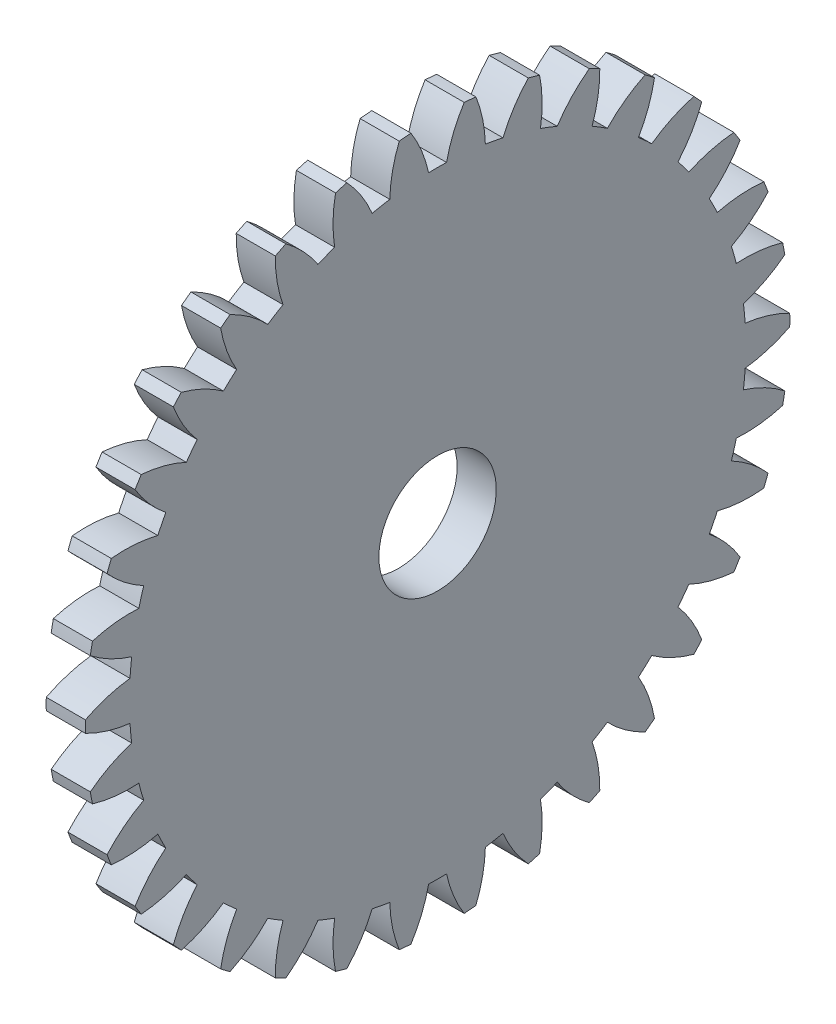
SolidWorks part; units mm, degrees
ref_plane "Plane1" through (0, 0, 0) normal (0, 0, 1) x (1, 0, 0)
ref_plane "Plane2" through (0, 0, 0) normal (0, 1, 0) x (1, 0, 0)
ref_plane "Plane3" through (0, 0, 0) normal (1, 0, 0) x (0, 0, -1)
sketch "HoldingSke" plane through (0, 0, 0) normal (0, 1, 0) x (1, 0, 0)
  line L0 (0, 0) -> (0.829, -0.5592)
  line L1 (-15, 0) -> (100, 0) construction
  line L2 (0, 0) -> (-2.1039, 2.3779)
  line L3 (0, 0) -> (-11.863, 4.5341)
  line L4 (0, 0) -> (7.1596, 4.8292)
  line L5 (0, 0) -> (-46.8476, -17.4728)
  line L6 (0, 0) -> (-1.6579, -1.1186)
  line L7 (-2.1039, 2.3779) -> (8.6586, 51.2059)
  line L8 (-76.2, 54.61) -> (-75.2, 54.61)
  line L9 (-71.009, 38.7566) -> (-53.1078, 45.2721)
  line L10 (-76.2, 71.12) -> (104.1128, 71.12)
  line L11 (0, 0) -> (-2, 0)
  line L12 (-76.2, 101.6) -> (-76.162, 101.6)
  line L13 (24.9733, 27.94) -> (52.9518, 28.4284)
  line L14 (24.9733, 27.94) -> (24.9743, 27.94)
  line L15 (24.9733, 27.94) -> (100.4006, 29.5858)
  line L16 (-63.627, -1) -> (-12.827, -1)
  circle A0 centre (0, 0) radius 3
  circle A1 centre (0, 0) radius 15.749
  circle A2 centre (0, 0) radius 37.5
  circle A3 centre (0, 0) radius 3
  dimension "MHD" = 31.498
  dimension "Hub_dia" = 75
  dimension "Bore" = 6
  dimension "MBD" = 6
  dimension "Num_teeth" = 34
  dimension "Pitch_radius" = 180.3128
  dimension "Pitch" = 1
  dimension "Width" = 2
  dimension "Overall_len" = 50
  dimension "Show_teeth" = 34
  dimension "Thickness" = 2
  dimension "OAL" = 50.0001
  dimension "T_dim" = 1
  dimension "Ap" = 20
  dimension "H" = 19.05
  dimension "Backlash" = 0.038
  dimension "Addendum_fac" = 1
  dimension "Dedendum_fac" = 1.25
  dimension "Clearance_fac" = 0.25
  dimension "Dedendum_add" = 0.001
  dimension "Module" = 1
sketch "BasProSke" plane through (0, 0, 0) normal (0, 1, 0) x (1, 0, 0)
  line L0 (-10, 0) -> (60, 0) construction
  line L1 (0, 0) -> (0, 18)
  line L2 (0, 0) -> (2, 0)
  line L3 (2, 0) -> (2, 18)
  line L4 (2, 18) -> (0, 18)
  dimension "Diameter" = 36
  dimension "Thickness" = 2
revolve "Base-Revolve" add sketch "BasProSke" angle 360 about L0
sketch "TooCutSke" plane through (0, 0, 0) normal (1, 0, 0) x (0, 0, -1)
  line L1 (0, 0) -> (0, 107) construction
  line L2 (0, 0) -> (-0.8516, 16.9787) construction
  line L3 (0, 0) -> (-3.1343, 33.8247) construction
  line L4 (-0.8516, 16.9787) -> (-1.5672, 16.9124) construction
  arc A0 (0.4581, 15.7423) -> (-0.4581, 15.7423) centre (0, 0) ccw
  arc A1 (1.3773, 17.9727) -> (-1.3773, 17.9727) centre (0, 0) ccw
  circle A2 centre (0, 0) radius 17 construction
  circle A3 centre (0, 0) radius 15.9748 construction
  arc A4 (-0.4581, 15.7423) -> (-1.3773, 17.9727) centre (-7.1051, 14.3077) ccw
  arc A5 (1.3773, 17.9727) -> (0.4581, 15.7423) centre (7.1051, 14.3077) ccw
  dimension "Root_dia" = 31.498
  dimension "Overcut_dia" = 36.0508
  dimension "Pitch_dia" = 34
  dimension "Base_dia" = 31.9495
  dimension "Flank_rad" = 6.8
  dimension "Half_ang" = 5.294
  dimension "Half_CT" = 0.7186
extrude "ToothCut" cut sketch "TooCutSke" along normal through all
fillet "Breaks" [suppressed] radius 0.02
fillet "RootFillets" [suppressed] radius 0.251
pattern_circular "TeethCuts" count 34 every 10.588 about axis through (-10, 0, 0) along (1, 0, 0) of "ToothCut", "RootFillets", "Breaks"
sketch "HubNeaOneSke" plane through (0, 0, 0) normal (-1, 0, 0) x (0, 0, 1)
  circle A0 centre (0, 0) radius 15.749
  dimension "Diameter" = 31.498
extrude "HubNearOne" [suppressed] add sketch "HubNeaOneSke" along normal blind 48.0001
sketch "HubNeaBotSke" plane through (0, 0, 0) normal (-1, 0, 0) x (0, 0, 1)
  circle A0 centre (0, 0) radius 15.749
  dimension "Diameter" = 31.498
extrude "HubNearBoth" [suppressed] add sketch "HubNeaBotSke" along normal blind 24
ref_plane "FarPln" through (2, 0, 0) normal (1, 0, 0) x (0, 0, -1)
sketch "HubFarSke" plane through (2, 0, 0) normal (1, 0, 0) x (0, 0, -1)
  circle A0 centre (0, 0) radius 15.749
  dimension "Diameter" = 31.498
extrude "HubFar" [suppressed] add sketch "HubFarSke" along normal blind 24
sketch "BorSke" plane through (0, 0, 0) normal (1, 0, 0) x (0, 0, -1)
  circle A0 centre (0, 0) radius 3
  dimension "Diameter" = 6
extrude "Bore" cut sketch "BorSke" along normal mid plane 100.0001
sketch "KeySke" plane through (0, 0, 0) normal (1, 0, 0) x (0, 0, -1)
  line L0 (-1, 0) -> (-1, 4)
  line L1 (-1, 4) -> (1, 4)
  line L2 (1, 4) -> (1, 0)
  line L3 (0, 0) -> (0, 34) construction
  line L4 (-1, 0) -> (1, 0)
  dimension "Offset" = 4
  dimension "Width" = 2
extrude "Keyway" [suppressed] cut sketch "KeySke" along normal mid plane 100.0001
pattern_circular "Keyway2" [suppressed] count 2 every 90 about axis through (-10, 0, 0) along (1, 0, 0)
equation "' \"Module@HoldingSke\" = 6.35"
equation "' \"Num_teeth@HoldingSke\" = 12"
equation "' \"Ap@HoldingSke\" =  20"
equation "' \"Width@HoldingSke\" = 0.5 * 25.4"
equation "' \"Hub_dia@HoldingSke\"= 1 * 25.4"
equation "' \"Overall_len@HoldingSke\" = 1.0 * 25.4"
equation "' \"Bore@HoldingSke\" = 0.75 * 25.4"
equation "' \"T_dim@HoldingSke\" = 0.1 * 25.4"
equation "' \"Width@KeySke\" = 0.25 * 25.4"
equation "' \"Show_teeth@HoldingSke\" = 13"
equation "' \"Backlash@HoldingSke\" = 0.009 * 25.4"
equation "' \"Addendum_fac@HoldingSke\" = 1.0"
equation "' \"Dedendum_fac@HoldingSke\" = 1.25"
equation "' \"Dedendum_add@HoldingSke\" = 0.00005 * 25.4"
equation "' \"Clearance_fac@HoldingSke\" = 0.25"
equation "\"Pitch@HoldingSke\" = 1 / \"Module@HoldingSke\""
equation "\"Overcut_dia@TooCutSke\" = (\"Num_teeth@HoldingSke\" + 2 * \"Addendum_fac@HoldingSke\") / \"Pitch@HoldingSke\" + 0.002 * 25.4"
equation "\"Pitch_dia@TooCutSke\" = \"Num_teeth@HoldingSke\" / \"Pitch@HoldingSke\""
equation "\"Base_dia@TooCutSke\" = \"Num_teeth@HoldingSke\" / \"Pitch@HoldingSke\" * cos((\"Ap@HoldingSke\"  * 3.14159265 / 180))"
equation "\"Root_dia@TooCutSke\" = (\"Num_teeth@HoldingSke\" + 2) / \"Pitch@HoldingSke\" - 2 * (\"Addendum_fac@HoldingSke\" + \"Dedendum_fac@HoldingSke\") / \"Pitch@HoldingSke\" - \"Dedendum_add@HoldingSke\" * 2"
equation "\"Half_ang@TooCutSke\" = 180 / \"Num_teeth@HoldingSke\""
equation "\"Half_CT@TooCutSke\" = \"Num_teeth@HoldingSke\" / \"Pitch@HoldingSke\" * sin((3.14159265 / 2 / \"Num_teeth@HoldingSke\")) / 2 - 7 * \"Backlash@HoldingSke\" / 4"
equation "\"Flank_rad@TooCutSke\" = \"Num_teeth@HoldingSke\" / \"Pitch@HoldingSke\" / 5"
equation "\"Radius@RootFillets\" = \"Clearance_fac@HoldingSke\" / \"Pitch@HoldingSke\" + \"Dedendum_add@HoldingSke\""
equation "\"Break_rad@Breaks\" = 0.02 / \"Pitch@HoldingSke\""
equation "\"Thickness@HoldingSke\" = \"Width@HoldingSke\""
equation "\"OAL@HoldingSke\" = \"Thickness@HoldingSke\""
equation "\"MHD@HoldingSke\" = (\"Num_teeth@HoldingSke\" + 2) / \"Pitch@HoldingSke\" - 2 * (\"Addendum_fac@HoldingSke\" + \"Dedendum_fac@HoldingSke\")  / \"Pitch@HoldingSke\" - \"Dedendum_add@HoldingSke\" * 2"
equation "\"MBD@HoldingSke\" = (\"Num_teeth@HoldingSke\" + 2) / \"Pitch@HoldingSke\" - 2 * (\"Addendum_fac@HoldingSke\" + \"Dedendum_fac@HoldingSke\")  / \"Pitch@HoldingSke\" - \"Dedendum_add@HoldingSke\" * 2 - 0.002 * 25.4"
equation "\"MHD@HoldingSke\" = ((sgn( \"MHD@HoldingSke\" - \"Hub_dia@HoldingSke\" )-1)*( \"MHD@HoldingSke\" - \"Hub_dia@HoldingSke\" ))/-2+ \"Hub_dia@HoldingSke\""
equation "\"MBD@HoldingSke\" = ((sgn( \"MBD@HoldingSke\" - \"Bore@HoldingSke\" )-1)*( \"MBD@HoldingSke\" - \"Bore@HoldingSke\" ))/-2+ \"Bore@HoldingSke\""
equation "\"OAL@HoldingSke\" = ((sgn( \"OAL@HoldingSke\" - \"Overall_len@HoldingSke\" )+1)*( \"OAL@HoldingSke\" - \"Overall_len@HoldingSke\" ))/2 + \"Overall_len@HoldingSke\" + 0.000002 * 25.4"
equation "\"Num_teeth@TeethCuts\" = int( \"Show_teeth@HoldingSke\" ) + 1"
equation "\"Num_teeth@TeethCuts\" = ((sgn( \"Num_teeth@TeethCuts\" - \"Num_teeth@HoldingSke\" )-1)*( \"Num_teeth@TeethCuts\" - \"Num_teeth@HoldingSke\" ))/-2+ \"Num_teeth@HoldingSke\""
equation "\"Num_teeth@TeethCuts\" = ((sgn( \"Num_teeth@TeethCuts\" - 2.0)+1)*( \"Num_teeth@TeethCuts\" - 2.0))/2 +2.0"
equation "\"Angle@TeethCuts\" = 360.0 / \"Num_teeth@HoldingSke\""
equation "\"Diameter@BasProSke\" = (\"Num_teeth@HoldingSke\" + 2 * \"Addendum_fac@HoldingSke\") / \"Pitch@HoldingSke\""
equation "\"Thickness@BasProSke\"  = \"Thickness@HoldingSke\""
equation "' \"Fillet_rad@BasProSke\" =  \"Thickness@HoldingSke\" * 0.05"
equation "\"MHD@HoldingSke\" = ((sgn( \"MHD@HoldingSke\" - \"Root_dia@TooCutSke\" )-1)*( \"MHD@HoldingSke\" - \"Root_dia@TooCutSke\" ))/-2+ \"Root_dia@TooCutSke\""
equation "\"Diameter@HubNeaOneSke\" = \"MHD@HoldingSke\""
equation "\"Length@HubNearOne\" = \"OAL@HoldingSke\" - \"Thickness@BasProSke\""
equation "\"Diameter@HubNeaBotSke\" = \"MHD@HoldingSke\""
equation "\"Length@HubNearBoth\" = ( \"OAL@HoldingSke\" - \"Thickness@BasProSke\" ) / 2.0"
equation "\"Thickness@FarPln\" = \"Thickness@BasProSke\""
equation "\"Diameter@HubFarSke\" = \"MHD@HoldingSke\""
equation "\"Length@HubFar\" = ( \"OAL@HoldingSke\" - \"Thickness@BasProSke\" ) / 2.0"
equation "\"Diameter@BorSke\" = \"MBD@HoldingSke\""
equation "\"D1@Bore\" = \"OAL@HoldingSke\" * 2.0"
equation "\"D1@Keyway\" = \"OAL@HoldingSke\" * 2.0"
equation "\"Offset@KeySke\" = \"T_dim@HoldingSke\" + \"MBD@HoldingSke\" / 2.0"
